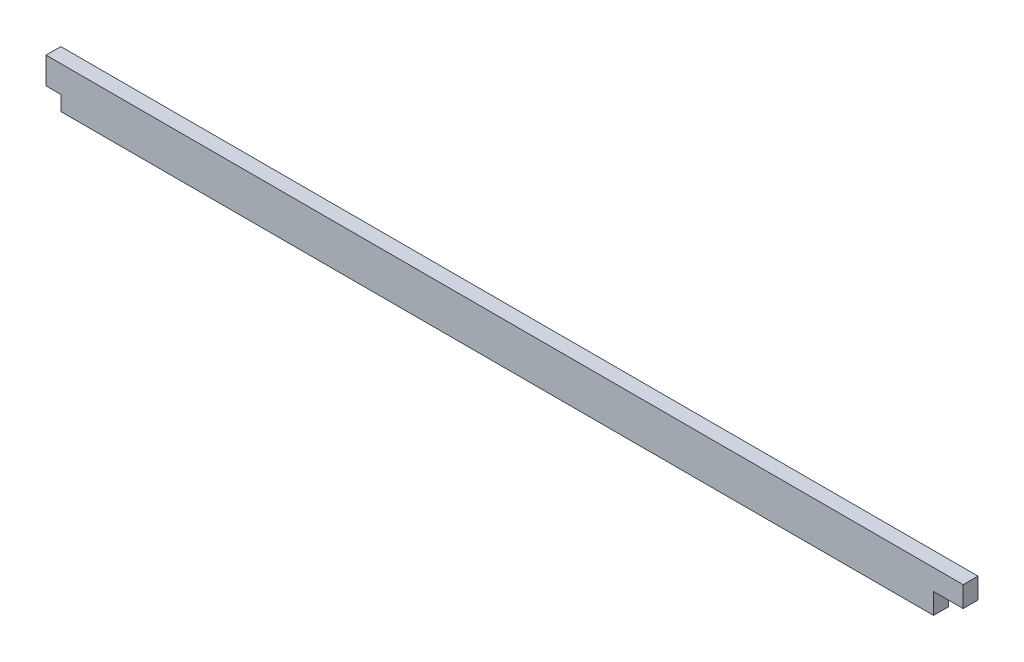
SolidWorks part; units mm, degrees
material "Фанера"
ref_plane "Front Plane" through (0, 0, 0) normal (0, 0, 1) x (1, 0, 0)
ref_plane "Top Plane" through (0, 0, 0) normal (0, 1, 0) x (1, 0, 0)
ref_plane "Right Plane" through (0, 0, 0) normal (1, 0, 0) x (0, 0, -1)
sketch "Эскиз1" plane through (0, 0, 0) normal (0, 0, 1) x (1, 0, 0)
  line L0 (86.7106, 0) -> (81.1106, 0)
  line L1 (-83.9106, -3.92) -> (81.1106, -3.92)
  line L3 (-43.0249, 3.92) -> (86.7106, 3.92)
  line L4 (86.7106, 0) -> (86.7106, 3.92)
  line L5 (-54.263, -2.4531) -> (86.7106, 3.92) construction
  line L6 (-86.7106, 3.92) -> (86.7106, -3.92) construction
  line L7 (81.1106, 0) -> (81.1106, -3.92)
  line L8 (-86.7106, -1.12) -> (-83.9106, -1.12)
  line L10 (-86.7106, -1.12) -> (-86.7106, 3.92)
  line L11 (-86.7106, 3.92) -> (-43.0249, 3.92)
  line L12 (-83.9106, -1.12) -> (-83.9106, -3.92)
  line L13 (-83.9106, -28.0356) -> (-83.9106, 3.7767) construction
  point P0 (0, 0)
  dimension "D2" = 7.84
  dimension "D3" = 5.6
  dimension "D1" = 2.8
  dimension "D4" = 2.8
extrude "Бобышка-Вытянуть1" add sketch "Эскиз1" along normal mid plane 2.8
equation "\"thickness\"= 2.8"
equation "\"D2@Эскиз1\"=\"thickness\"+\"thickness\"*1.8"
equation "\"D3@Эскиз1\"=\"thickness\"*2"
equation "\"D1@Бобышка-Вытянуть1\"=\"thickness\""
equation "\"D1@Эскиз1\"=\"thickness\""
equation "\"D4@Эскиз1\"=\"thickness\""
